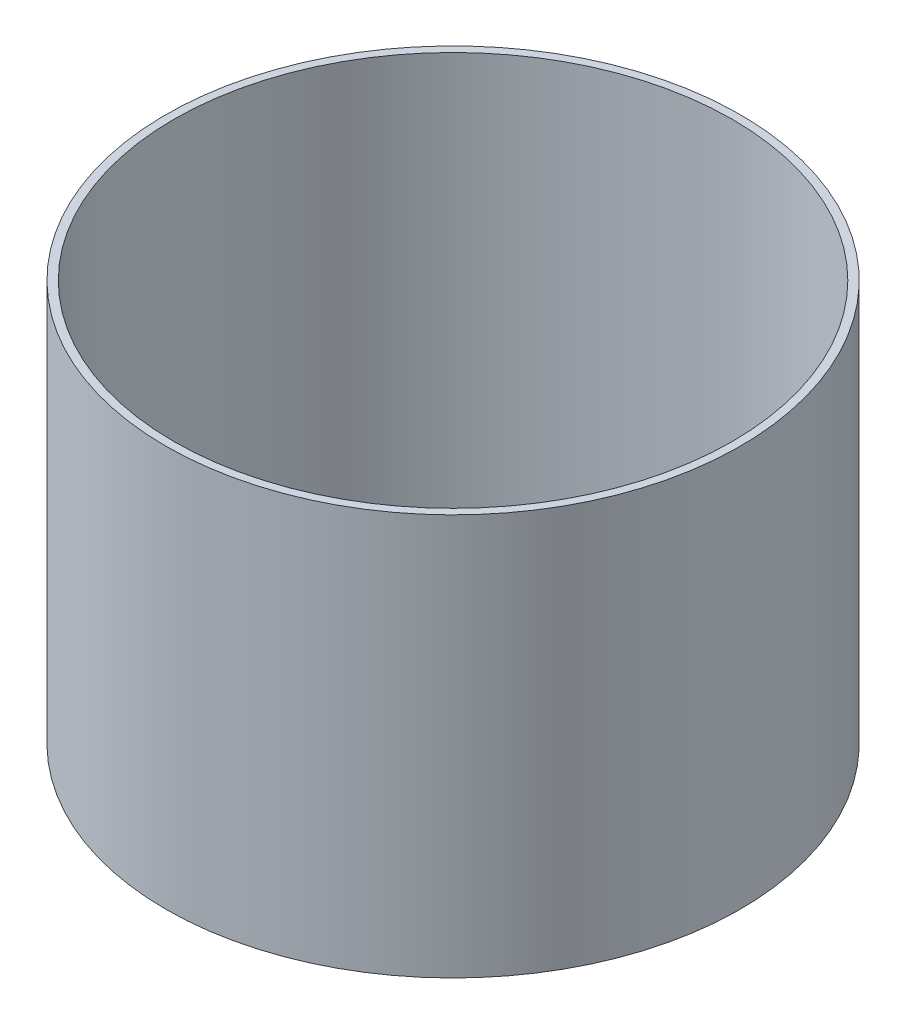
SolidWorks part; units mm, degrees
ref_plane "Front Plane" through (0, 0, 0) normal (0, 0, 1) x (1, 0, 0)
ref_plane "Top Plane" through (0, 0, 0) normal (0, 1, 0) x (1, 0, 0)
ref_plane "Right Plane" through (0, 0, 0) normal (1, 0, 0) x (0, 0, -1)
sketch "Sketch1" plane through (0, 0, 0) normal (0, 1, 0) x (1, 0, 0)
  circle A0 centre (0, 0) radius 8.7
  circle A1 centre (0, 0) radius 8.95
  point P5 (0, 0)
  dimension "D1" = 0.25
  dimension "D2" = 17.4
extrude "Boss-Extrude1" add sketch "Sketch1" along normal blind 12.5
